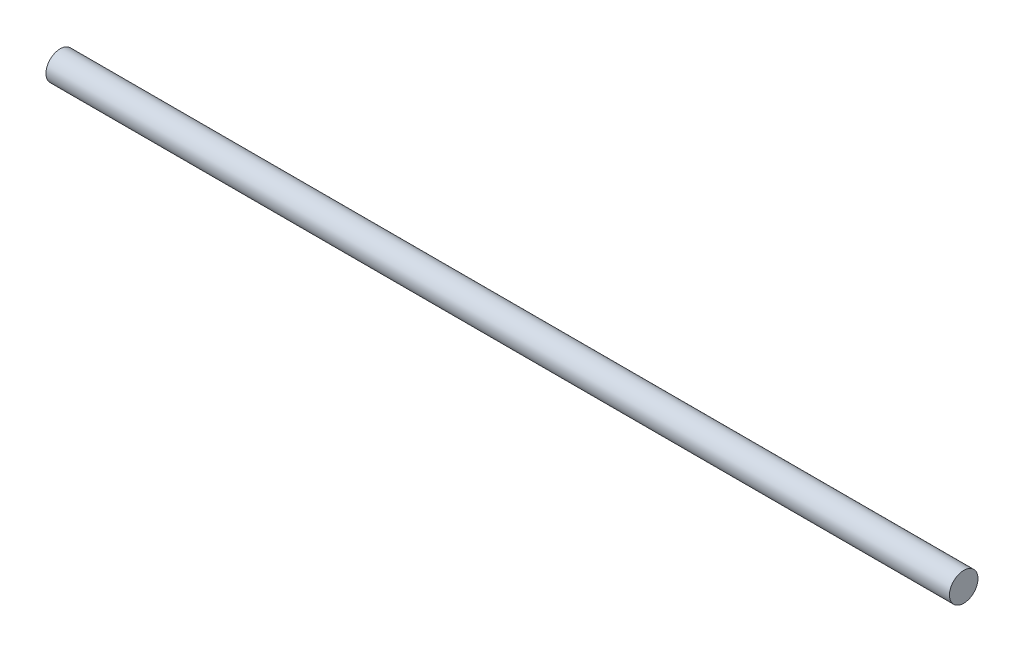
SolidWorks part; units mm, degrees
ref_plane "Front Plane" through (0, 0, 0) normal (0, 0, 1) x (1, 0, 0)
ref_plane "Top Plane" through (0, 0, 0) normal (0, 1, 0) x (1, 0, 0)
ref_plane "Right Plane" through (0, 0, 0) normal (1, 0, 0) x (0, 0, -1)
sketch "Sketch1" plane through (0, 0, 0) normal (1, 0, 0) x (0, 0, -1)
  circle A0 centre (0, 0) radius 3
  dimension "D1" = 6
extrude "Boss-Extrude1" add sketch "Sketch1" along normal blind 190
